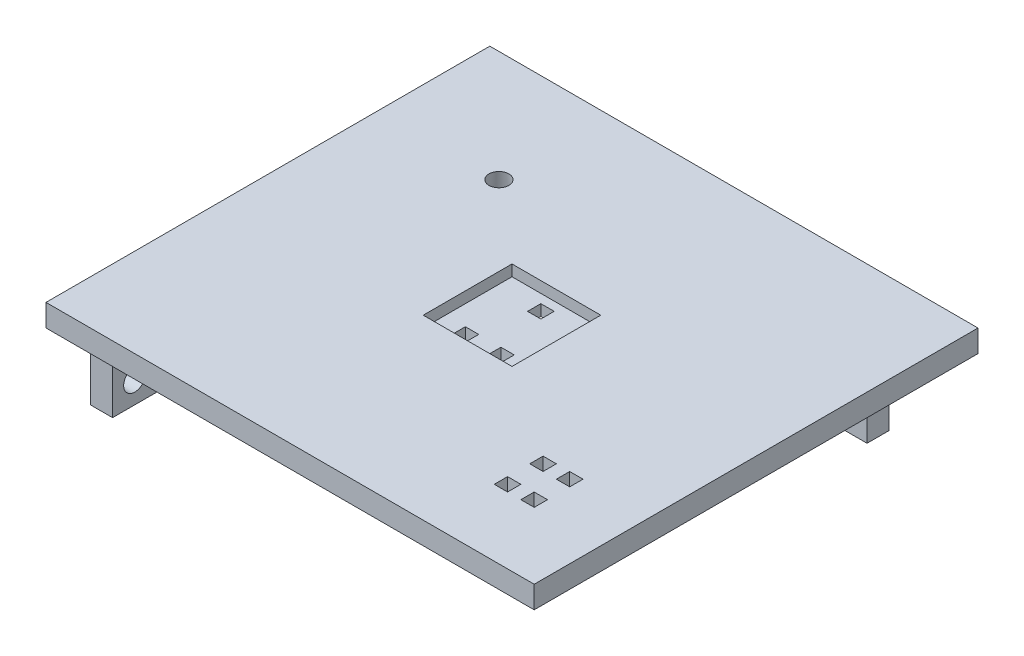
SolidWorks part; units mm, degrees
ref_plane "Front Plane" through (0, 0, 0) normal (0, 0, 1) x (1, 0, 0)
ref_plane "Top Plane" through (0, 0, 0) normal (0, 1, 0) x (1, 0, 0)
ref_plane "Right Plane" through (0, 0, 0) normal (1, 0, 0) x (0, 0, -1)
sketch "Sketch1" plane through (0, 0, 0) normal (0, 1, 0) x (1, 0, 0)
  line L0 (-57.5, 45) -> (-52.5, 45) construction
  line L1 (-110, 100) -> (0, 100)
  line L2 (-110, 100) -> (-110, 0)
  line L3 (-110, 0) -> (0, 0)
  line L4 (0, 100) -> (0, 0)
  line L5 (-60.5, 42) -> (-57.5, 42)
  line L6 (-60.5, 42) -> (-60.5, 45)
  line L7 (-60.5, 45) -> (-57.5, 45)
  line L8 (-57.5, 42) -> (-57.5, 45)
  line L9 (-52.5, 42) -> (-49.5, 42)
  line L10 (-52.5, 42) -> (-52.5, 45)
  line L11 (-52.5, 45) -> (-49.5, 45)
  line L12 (-49.5, 42) -> (-49.5, 45)
  line L13 (-56.5, 55) -> (-53.5, 55)
  line L14 (-56.5, 55) -> (-56.5, 58)
  line L15 (-56.5, 58) -> (-53.5, 58)
  line L16 (-53.5, 55) -> (-53.5, 58)
  line L17 (-55, 45) -> (-55, 55) construction
  point P17 (-52.5, 43.5)
  point P18 (-55, 45)
  point P19 (-55, 55)
  point P23 (-55, 0)
  point P24 (0, 50)
  point P25 (-55, 50)
  dimension "D1" = 110
  dimension "D2" = 100
  dimension "D3" = 3
  dimension "D4" = 3
  dimension "D5" = 3
  dimension "D6" = 3
  dimension "D7" = 3
  dimension "D8" = 3
  dimension "D9" = 5
  dimension "D10" = 10
extrude "Boss-Extrude1" add sketch "Sketch1" along normal blind 2.5
sketch "Sketch2" plane through (0, 2.5, 0) normal (0, 1, 0) x (1, 0, 0)
  line L1 (-110, 100) -> (0, 100)
  line L2 (-110, 100) -> (-110, 0)
  line L3 (-110, 0) -> (0, 0)
  line L4 (0, 100) -> (0, 0)
  line L5 (-65, 60) -> (-45, 60)
  line L6 (-65, 60) -> (-65, 40)
  line L7 (-65, 40) -> (-45, 40)
  line L8 (-45, 60) -> (-45, 40)
  point P11 (-55, 100)
  point P12 (-55, 60)
  point P13 (-45, 50)
  point P14 (0, 50)
  dimension "D1" = 20
  dimension "D2" = 20
extrude "Boss-Extrude2" add sketch "Sketch2" along normal blind 2.5
sketch "Sketch3" plane through (0, 5, 0) normal (0, 1, 0) x (1, 0, 0)
  circle A0 centre (-82.9212, 74.9754) radius 2.25
  dimension "D1" = 4.5
extrude "Cut-Extrude1" cut sketch "Sketch3" against normal through all draft 8 draft outward yes
sketch "Sketch4" plane through (0, 5, 0) normal (0, 1, 0) x (1, 0, 0)
  line L1 (-24, 26) -> (-21, 26)
  line L2 (-24, 26) -> (-24, 23)
  line L3 (-24, 23) -> (-21, 23)
  line L4 (-21, 26) -> (-21, 23)
  line L5 (-18, 26) -> (-15, 26)
  line L6 (-18, 26) -> (-18, 23)
  line L7 (-18, 23) -> (-15, 23)
  line L8 (-15, 26) -> (-15, 23)
  line L9 (-24, 18) -> (-21, 18)
  line L10 (-24, 18) -> (-24, 15)
  line L11 (-24, 15) -> (-21, 15)
  line L12 (-21, 18) -> (-21, 15)
  line L13 (-18, 18) -> (-15, 18)
  line L14 (-18, 18) -> (-18, 15)
  line L15 (-18, 15) -> (-15, 15)
  line L16 (-15, 18) -> (-15, 15)
  line L17 (0, 0) -> (0, 100) construction
  line L18 (-110, 0) -> (0, 0) construction
  dimension "D1" = 3
  dimension "D2" = 3
  dimension "D3" = 3
  dimension "D4" = 3
  dimension "D5" = 3
  dimension "D6" = 3
  dimension "D7" = 3
  dimension "D8" = 3
  dimension "D9" = 3
  dimension "D10" = 3
  dimension "D11" = 5
  dimension "D12" = 5
  dimension "D13" = 15
  dimension "D14" = 15
extrude "Cut-Extrude2" cut sketch "Sketch4" against normal through all
sketch "Sketch5" plane through (0, 5, 0) normal (0, 1, 0) x (1, 0, 0)
  line L1 (-20, 90) -> (-10, 90)
  line L2 (-20, 90) -> (-20, 85)
  line L3 (-20, 85) -> (-10, 85)
  line L4 (-10, 90) -> (-10, 85)
  line L5 (0, 100) -> (-110, 100) construction
  line L6 (0, 0) -> (0, 100) construction
  dimension "D1" = 5
  dimension "D2" = 10
  dimension "D3" = 10
  dimension "D4" = 10
extrude "Boss-Extrude3" add sketch "Sketch5" against normal blind 20
sketch "Sketch8" plane through (0, 0, -90) normal (0, 0, -1) x (-1, 0, 0)
  line L0 (10, -15) -> (20, -15) construction
  line L1 (10, 0) -> (20, 0) construction
  circle A0 centre (15, -10) radius 2.5
  point P4 (15, -15)
  dimension "D1" = 5
  dimension "D2" = 10
extrude "Cut-Extrude4" cut sketch "Sketch8" against normal blind 15
sketch "Sketch9" plane through (0, 0, 0) normal (0, -1, 0) x (1, 0, 0)
  line L0 (-110, -100) -> (-110, 0) construction
  line L1 (-105, -5) -> (-100, -5)
  line L2 (-105, -5) -> (-105, -15)
  line L3 (-105, -15) -> (-100, -15)
  line L4 (-100, -5) -> (-100, -15)
  line L5 (-110, 0) -> (0, 0) construction
  dimension "D1" = 5
  dimension "D2" = 10
  dimension "D3" = 5
  dimension "D4" = 5
extrude "Boss-Extrude4" add sketch "Sketch9" along normal blind 15
sketch "Sketch10" plane through (-105, 0, 0) normal (-1, 0, 0) x (0, 0, 1)
  line L0 (-5, -15) -> (-15, -15) construction
  line L1 (-5, 0) -> (-15, 0) construction
  circle A0 centre (-10, -10) radius 2.5
  point P4 (-10, -15)
  dimension "D1" = 5
  dimension "D2" = 10
extrude "Cut-Extrude5" cut sketch "Sketch10" against normal blind 15 contours A0
